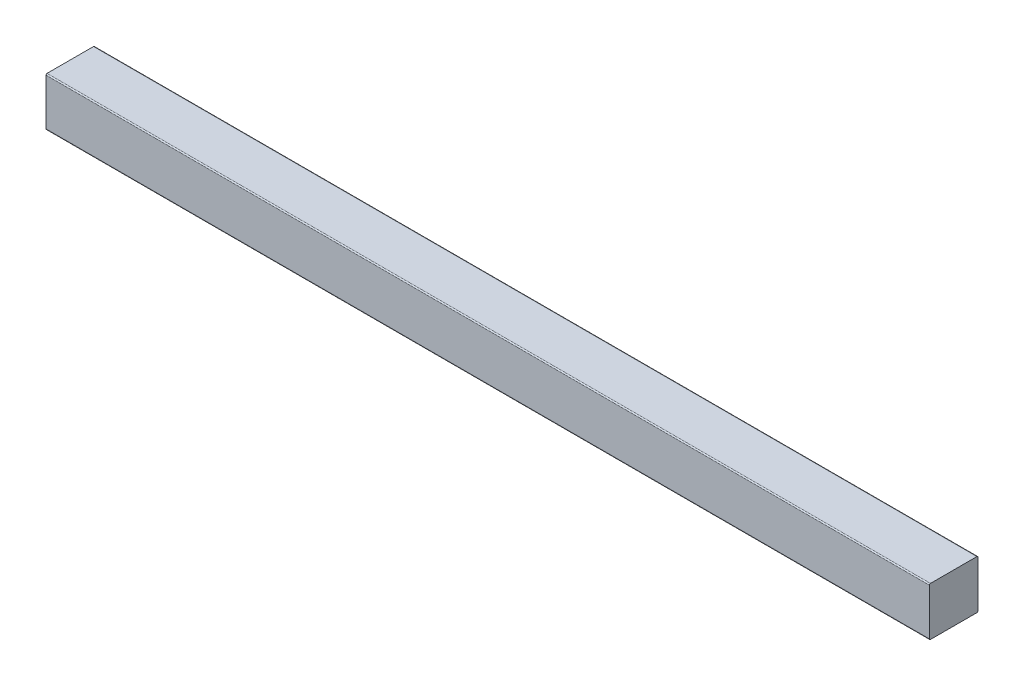
SolidWorks part; units mm, degrees
ref_plane "Front Plane" through (0, 0, 0) normal (0, 0, 1) x (1, 0, 0)
ref_plane "Top Plane" through (0, 0, 0) normal (0, 1, 0) x (1, 0, 0)
ref_plane "Right Plane" through (0, 0, 0) normal (1, 0, 0) x (0, 0, -1)
sketch "Sketch1" plane through (0, 0, 0) normal (1, 0, 0) x (0, 0, -1)
  line L1 (0, 0) -> (44, 0)
  line L2 (0, 0) -> (0, 44)
  line L3 (0, 44) -> (44, 44)
  line L4 (44, 0) -> (44, 44)
  dimension "D1" = 44
extrude "Boss-Extrude1" add sketch "Sketch1" along normal blind 800
fillet "Fillet1" radius 1 4 edges at (400, 0, -44) (400, 0, 0) (400, 44, -44) (400, 44, 0)
